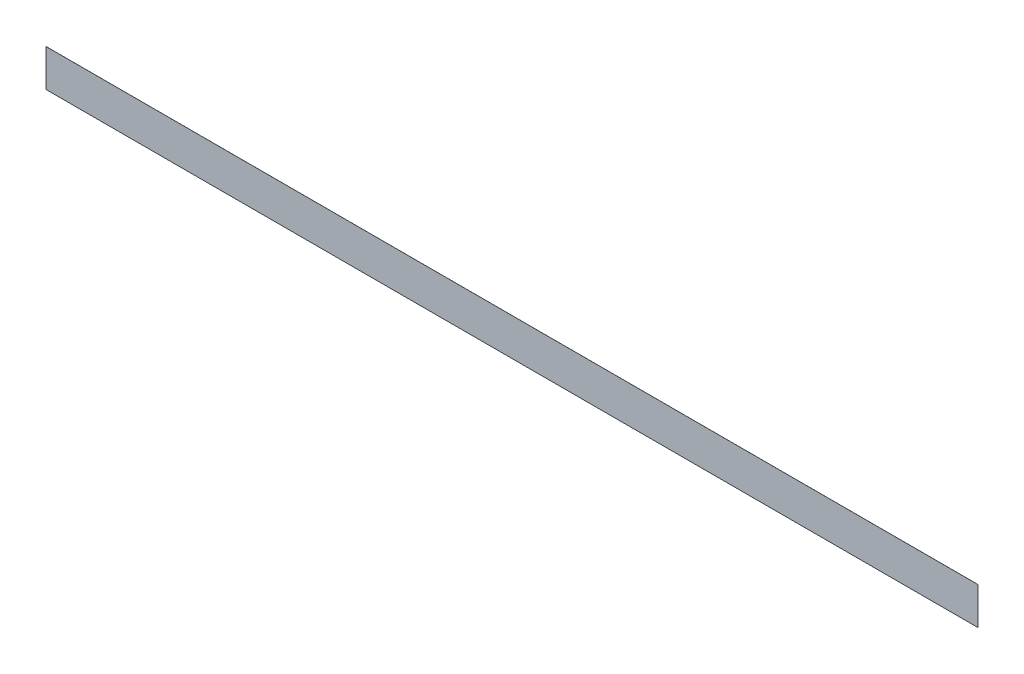
SolidWorks part; units mm, degrees
ref_plane "Front Plane" through (0, 0, 0) normal (0, 0, 1) x (1, 0, 0)
ref_plane "Top Plane" through (0, 0, 0) normal (0, 1, 0) x (1, 0, 0)
ref_plane "Right Plane" through (0, 0, 0) normal (1, 0, 0) x (0, 0, -1)
sketch "Sketch1" plane through (0, 0, 0) normal (0, 0, 1) x (1, 0, 0)
  line L1 (-125000, 5000) -> (125000, 5000)
  line L2 (-125000, 5000) -> (-125000, -5000)
  line L3 (-125000, -5000) -> (125000, -5000)
  line L4 (125000, 5000) -> (125000, -5000)
  line L5 (-125000, 5000) -> (125000, -5000) construction
  line L6 (-125000, -5000) -> (125000, 5000) construction
  point P0 (0, 0)
  dimension "D1" = 250000
  dimension "D2" = 10000
extrude "Boss-Extrude1" add sketch "Sketch1" along normal blind 10 contours L2 L1 L4 L3
